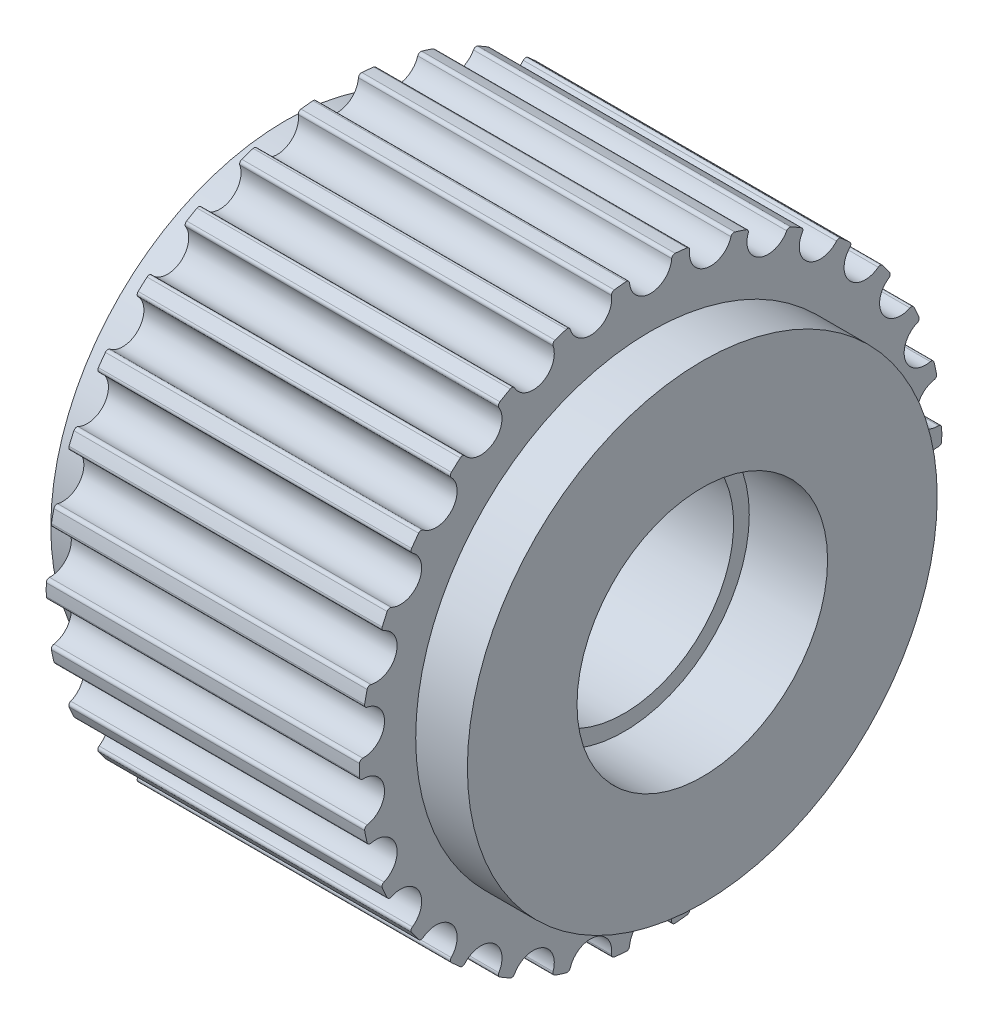
SolidWorks part; units mm, degrees
ref_plane "Front Plane" through (0, 0, 0) normal (0, 0, 1) x (1, 0, 0)
ref_plane "Top Plane" through (0, 0, 0) normal (0, 1, 0) x (1, 0, 0)
ref_plane "Right Plane" through (0, 0, 0) normal (1, 0, 0) x (0, 0, -1)
sketch "Sketch1" plane through (0, 0, 0) normal (0, 0, 1) x (1, 0, 0)
  line L0 (0, 0) -> (13.3, 0) construction
  line L1 (0, 4) -> (2.5, 4)
  line L2 (2.5, 4) -> (2.5, 3.5)
  line L3 (2.5, 3.5) -> (10.8, 3.5)
  line L4 (10.8, 3.5) -> (10.8, 4)
  line L5 (10.8, 4) -> (13.3, 4)
  line L6 (13.3, 4) -> (13.3, 7.5)
  line L7 (13.3, 7.5) -> (11.65, 7.5)
  line L8 (11.65, 7.5) -> (11.65, 9.295)
  line L9 (11.65, 9.295) -> (1.65, 9.295)
  line L10 (1.65, 9.295) -> (1.65, 7.5)
  line L11 (1.65, 7.5) -> (0, 7.5)
  line L12 (0, 7.5) -> (0, 4)
  line L13 (1.65, 9.55) -> (11.65, 9.55) construction
  line L14 (0, 2.5) -> (13.3, 2.5) construction
  dimension "W" = 13.3
  dimension "A" = 10
  dimension "Dh" = 7
  dimension "D" = 8
  dimension "E" = 15
  dimension "O.D." = 18.59
  dimension "P.D." = 19.1
  dimension "D_s" = 5
revolve "Revolve1" add sketch "Sketch1" angle 360 about L0
sketch "Sketch2" [suppressed] plane through (2.2, 0, 0) normal (1, 0, 0) x (0, 0, -1)
  line L0 (0, 0) -> (0, 21.71) construction
  line L2 (-0.7244, 19.8868) -> (-1.66, 21.6464)
  line L3 (0.7244, 19.8868) -> (1.66, 21.6464)
  circle A1 centre (0, 0) radius 21.71 construction
  circle A3 centre (0, 0) radius 19.9 construction
  circle A4 centre (0, 0) radius 22.281 construction
  arc A9 (-1.66, 21.6464) -> (1.66, 21.6464) centre (0, 0) cw
  arc A10 (-0.7244, 19.8868) -> (0.7244, 19.8868) centre (0, 0) cw
  dimension "MSM_6" = 3.32
  dimension "MSM_7" = 28
  dimension "MSM_1" = 0.75
  dimension "MSM_2" = 0.254
extrude "Cut-Extrude1" [suppressed] cut sketch "Sketch2" along normal through all
fillet "Fillet1" [suppressed] radius 0.2
fillet "Fillet2" [suppressed] radius 0.2
pattern_circular "CirPattern1" [suppressed] count 30 over 360
sketch "Sketch3" plane through (0, 0, 0) normal (-1, 0, 0) x (0, 0, 1)
  line L0 (0, 0) -> (0, 9.22) construction
  circle A0 centre (0, 0) radius 8.545 construction
  circle A1 centre (0, 0) radius 9.549 construction
  circle A2 centre (0, 0) radius 9.295 construction
  arc A3 (-0.6731, 9.2706) -> (0.6731, 9.2706) centre (0, 9.22) ccw
  arc A8 (-0.6731, 9.2706) -> (0.6731, 9.2706) centre (0, 0) cw
  dimension "O.D." = 18.59
  dimension "MSM_10" = 0.675
  dimension "MSM_1" = 0.75
  dimension "MSM_2" = 0.254
extrude "Cut-Extrude2" cut sketch "Sketch3" against normal through all
fillet "Fillet3" radius 0.1 2 edges at (6.65, 9.2706, -0.6731) (6.65, 9.2706, 0.6731)
pattern_circular "CirPattern2" count 30 over 360 about axis through (0, 0, 0) along (1, 0, 0) of "Cut-Extrude2", "Fillet3"
